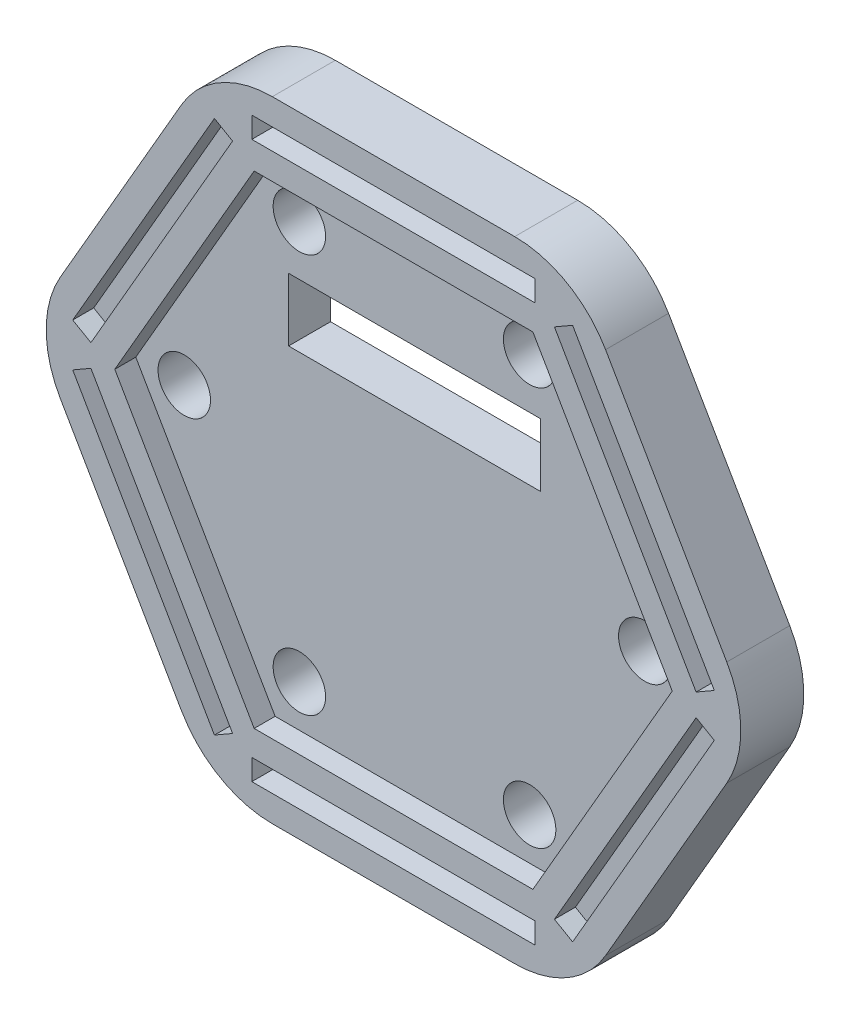
SolidWorks part; units mm, degrees
ref_plane "Front" through (0, 0, 0) normal (0, 0, 1) x (1, 0, 0)
ref_plane "Top" through (0, 0, 0) normal (0, 1, 0) x (1, 0, 0)
ref_plane "Right" through (0, 0, 0) normal (1, 0, 0) x (0, 0, -1)
sketch "Эскиз1" plane through (0, 0, 0) normal (0, 0, 1) x (1, 0, 0)
  line L1 (8.6603, 15) -> (-8.6603, 15)
  line L2 (-8.6603, 15) -> (-17.3205, 0)
  line L3 (-17.3205, 0) -> (-8.6603, -15)
  line L4 (-8.6603, -15) -> (8.6603, -15)
  line L5 (8.6603, -15) -> (17.3205, 0)
  line L6 (17.3205, 0) -> (8.6603, 15)
  circle A0 centre (0, 0) radius 15 construction
  dimension "D1" = 30
extrude "Бобышка-Вытянуть1" add sketch "Эскиз1" along normal blind 2
sketch "Эскиз2" plane through (0, 0, 2) normal (0, 0, 1) x (1, 0, 0)
  line L1 (7.9386, 13.75) -> (-7.9386, 13.75)
  line L2 (-7.9386, 13.75) -> (-15.8771, 0)
  line L3 (-15.8771, 0) -> (-7.9386, -13.75)
  line L4 (-7.9386, -13.75) -> (7.9386, -13.75)
  line L5 (7.9386, -13.75) -> (15.8771, 0)
  line L6 (15.8771, 0) -> (7.9386, 13.75)
  line L7 (8.6603, 15) -> (-8.6603, 15)
  line L8 (-8.6603, 15) -> (-17.3205, 0)
  line L9 (-17.3205, 0) -> (-8.6603, -15)
  line L10 (-8.6603, -15) -> (8.6603, -15)
  line L11 (8.6603, -15) -> (17.3205, 0)
  line L12 (17.3205, 0) -> (8.6603, 15)
  circle A0 centre (0, 0) radius 13.75 construction
  circle A1 centre (0, 0) radius 15 construction
  point P1 (-17.3205, 0)
  dimension "D1" = 27.5
extrude "Бобышка-Вытянуть2" add sketch "Эскиз2" along normal blind 1
sketch "Эскиз3" plane through (0, 0, 2) normal (0, 0, 1) x (1, 0, 0)
  line L0 (-7.9386, 13.75) -> (-15.8771, 0) construction
  line L1 (6.6395, 11.5) -> (-6.6395, 11.5)
  line L2 (-6.6395, 11.5) -> (-13.2791, 0)
  line L3 (-13.2791, 0) -> (-6.6395, -11.5)
  line L4 (-6.6395, -11.5) -> (6.6395, -11.5)
  line L5 (6.6395, -11.5) -> (13.2791, 0)
  line L6 (13.2791, 0) -> (6.6395, 11.5)
  line L7 (7.3612, 12.75) -> (-7.3612, 12.75)
  line L8 (-7.3612, 12.75) -> (-14.7224, 0)
  line L9 (-14.7224, 0) -> (-7.3612, -12.75)
  line L10 (-7.3612, -12.75) -> (7.3612, -12.75)
  line L11 (7.3612, -12.75) -> (14.7224, 0)
  line L12 (14.7224, 0) -> (7.3612, 12.75)
  circle A0 centre (0, 0) radius 11.5 construction
  circle A1 centre (0, 0) radius 12.75 construction
  dimension "D1" = 1
  dimension "D2" = 1.25
extrude "Бобышка-Вытянуть3" add sketch "Эскиз3" along normal blind 1
sketch "Эскиз4" plane through (0, 0, 2) normal (0, 0, 1) x (1, 0, 0)
  line L0 (8.6603, 15) -> (-8.6603, 15) construction
  line L1 (-6, 4.1) -> (6, 4.1)
  line L2 (-6, 4.1) -> (-6, 7.1)
  line L3 (-6, 7.1) -> (6, 7.1)
  line L4 (6, 4.1) -> (6, 7.1)
  line L5 (-6, 4.1) -> (6, 7.1) construction
  line L6 (-6, 7.1) -> (6, 4.1) construction
  point P0 (0, 5.6)
  dimension "D1" = 9.4
  dimension "D2" = 3
  dimension "D3" = 12
extrude "Вырез-Вытянуть1" cut sketch "Эскиз4" against normal through all
sketch "Эскиз5" plane through (0, 0, 2) normal (0, 0, 1) x (1, 0, 0)
  line L1 (5.4848, 9.5) -> (-5.4848, 9.5) construction
  line L2 (-5.4848, 9.5) -> (-10.9697, 0) construction
  line L3 (-10.9697, 0) -> (-5.4848, -9.5) construction
  line L4 (-5.4848, -9.5) -> (5.4848, -9.5) construction
  line L5 (5.4848, -9.5) -> (10.9697, 0) construction
  line L6 (10.9697, 0) -> (5.4848, 9.5) construction
  circle A0 centre (0, 0) radius 9.5 construction
  circle A1 centre (-5.4848, 9.5) radius 1.25
  circle A2 centre (5.4848, 9.5) radius 1.25
  circle A3 centre (10.9697, 0) radius 1.25
  circle A4 centre (5.4848, -9.5) radius 1.25
  circle A5 centre (-5.4848, -9.5) radius 1.25
  circle A6 centre (-10.9697, 0) radius 1.25
  dimension "D2" = 2.5
  dimension "D1" = 19
extrude "Вырез-Вытянуть2" cut sketch "Эскиз5" against normal through all
sketch "Эскиз6" plane through (0, 0, 2) normal (0, 0, 1) x (1, 0, 0)
  line L1 (8.6603, 15) -> (-8.6603, 15)
  line L2 (-8.6603, 15) -> (-17.3205, 0)
  line L3 (-17.3205, 0) -> (-8.6603, -15)
  line L4 (-8.6603, -15) -> (8.6603, -15)
  line L5 (8.6603, -15) -> (17.3205, 0)
  line L6 (17.3205, 0) -> (8.6603, 15)
  line L7 (6.6395, 11.5) -> (-6.6395, 11.5)
  line L8 (-6.6395, 11.5) -> (-13.2791, 0)
  line L9 (-13.2791, 0) -> (-6.6395, -11.5)
  line L10 (-6.6395, -11.5) -> (6.6395, -11.5)
  line L11 (6.6395, -11.5) -> (13.2791, 0)
  line L12 (13.2791, 0) -> (6.6395, 11.5)
  circle A0 centre (0, 0) radius 15 construction
  circle A1 centre (0, 0) radius 11.5 construction
  point P1 (-13.2791, 0)
  point P18 (-17.3205, 0)
extrude "Бобышка-Вытянуть4" [suppressed] add sketch "Эскиз6" along normal blind 3
sketch "Эскиз7" plane through (0, 0, 3) normal (0, 0, 1) x (1, 0, 0)
  line L0 (-6.75, 11.6913) -> (-9.6154, 13.3457)
  line L2 (-8.6603, 15) -> (-17.3205, 0) construction
  line L3 (-9.6154, 13.3457) -> (-8.6603, 15)
  line L4 (-8.6603, 15) -> (-6.75, 15)
  line L5 (8.6603, 15) -> (-8.6603, 15) construction
  line L6 (-6.75, 15) -> (-6.75, 11.6913)
  line L10 (6.75, 11.6913) -> (6.75, 15)
  line L11 (6.75, 15) -> (8.6603, 15)
  line L12 (8.6603, 15) -> (9.6154, 13.3457)
  line L13 (9.6154, 13.3457) -> (6.75, 11.6913)
  line L14 (13.5, 0) -> (16.3654, 1.6543)
  line L15 (16.3654, 1.6543) -> (17.3205, 0)
  line L16 (17.3205, 0) -> (16.3654, -1.6543)
  line L17 (16.3654, -1.6543) -> (13.5, 0)
  line L18 (6.75, -11.6913) -> (9.6154, -13.3457)
  line L19 (9.6154, -13.3457) -> (8.6603, -15)
  line L20 (8.6603, -15) -> (6.75, -15)
  line L21 (6.75, -15) -> (6.75, -11.6913)
  line L22 (-6.75, -11.6913) -> (-6.75, -15)
  line L23 (-6.75, -15) -> (-8.6603, -15)
  line L24 (-8.6603, -15) -> (-9.6154, -13.3457)
  line L25 (-9.6154, -13.3457) -> (-6.75, -11.6913)
  line L26 (-13.5, 0) -> (-16.3654, -1.6543)
  line L27 (-16.3654, -1.6543) -> (-17.3205, 0)
  line L28 (-17.3205, 0) -> (-16.3654, 1.6543)
  line L29 (-16.3654, 1.6543) -> (-13.5, 0)
  point P6 (8.6603, 15)
  point P32 (0, 0)
  dimension "D1" = 6
  dimension "D2" = 13.5
extrude "Бобышка-Вытянуть5" add sketch "Эскиз7" against normal through all
fillet "Скругление1" radius 5 6 edges at (-8.6603, 15, 1.5) (8.6603, 15, 1.5) (17.3205, 0, 1.5) (8.6603, -15, 1.5) (-8.6603, -15, 1.5) (-17.3205, 0, 1.5)
